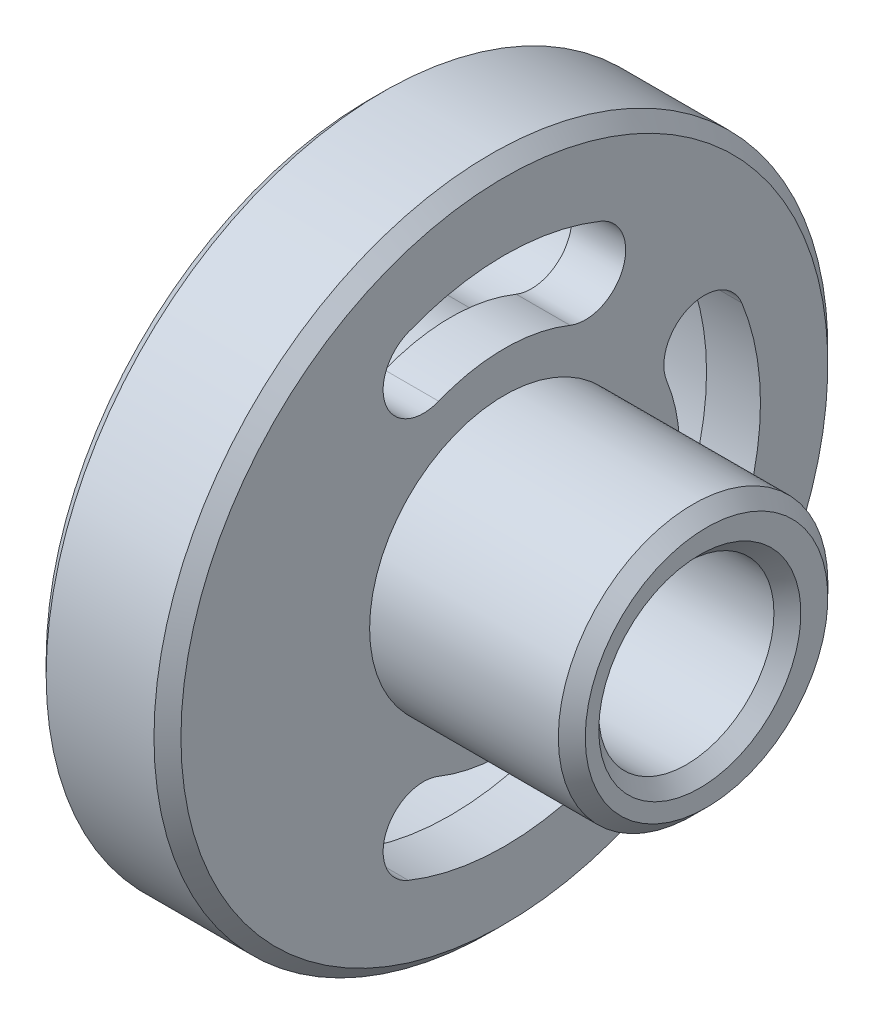
SolidWorks part; units mm, degrees
ref_plane "Спереди" through (0, 0, 0) normal (0, 0, 1) x (1, 0, 0)
ref_plane "Сверху" through (0, 0, 0) normal (0, 1, 0) x (1, 0, 0)
ref_plane "Справа" through (0, 0, 0) normal (1, 0, 0) x (0, 0, -1)
other "Configuration Table"
sketch "Эскиз1" plane through (0, 0, 0) normal (0, 0, 1) x (1, 0, 0)
  line L6 (0, 0) -> (24.4592, 0) construction
  line L7 (0, 0) -> (0, 24)
  line L8 (1, 25) -> (9, 25)
  line L9 (10, 24) -> (10, 10)
  line L10 (10, 10) -> (24, 10)
  line L11 (25, 9) -> (25, 0)
  line L12 (25, 0) -> (0, 0)
  line L13 (0, 24) -> (1, 25)
  line L14 (9, 25) -> (10, 24)
  line L15 (24, 10) -> (25, 9)
  point P4 (0, 25)
  point P5 (10, 25)
  point P7 (25, 10)
  dimension "D1" = 20
  dimension "D2" = 50
  dimension "D3" = 10
  dimension "D4" = 25
revolve "Повернуть1" add sketch "Эскиз1" angle 360 about L6
sketch "Эскиз3" plane through (25, 0, 0) normal (1, 0, 0) x (0, 0, -1)
  line L0 (0, 0) -> (8.7913, 0) construction
  circle A0 centre (-0.5, 0) radius 6.5
  dimension "D1" = 13
  dimension "D2" = 0.5
sketch "Эскиз4" plane through (0, 0, 0) normal (-1, 0, 0) x (0, 0, 1)
  line L0 (-8.7913, 0) -> (27.3062, 0) construction
  line L1 (0, 0) -> (0, 21.7955) construction
  line L2 (0, 0) -> (4.125, 10.1973) construction
  arc A0 (6, 14.8324) -> (-6, 14.8324) centre (0, 0) ccw construction
  arc A5 (7.875, 19.4675) -> (-7.875, 19.4675) centre (0, 0) ccw
  arc A6 (4.125, 10.1973) -> (-4.125, 10.1973) centre (0, 0) ccw
  arc A7 (4.125, 10.1973) -> (7.875, 19.4675) centre (6, 14.8324) ccw
  arc A8 (-7.875, 19.4675) -> (-4.125, 10.1973) centre (-6, 14.8324) ccw
  arc A9 (-10.1973, 4.125) -> (-10.1973, -4.125) centre (0, 0) ccw
  arc A10 (-10.1973, 4.125) -> (-19.4675, 7.875) centre (-14.8324, 6) ccw
  arc A11 (-19.4675, -7.875) -> (-10.1973, -4.125) centre (-14.8324, -6) ccw
  arc A12 (-19.4675, 7.875) -> (-19.4675, -7.875) centre (0, 0) ccw
  arc A13 (-14.8324, 6) -> (-14.8324, -6) centre (0, 0) ccw construction
  arc A14 (-4.125, -10.1973) -> (4.125, -10.1973) centre (0, 0) ccw
  arc A15 (-4.125, -10.1973) -> (-7.875, -19.4675) centre (-6, -14.8324) ccw
  arc A16 (7.875, -19.4675) -> (4.125, -10.1973) centre (6, -14.8324) ccw
  arc A17 (-7.875, -19.4675) -> (7.875, -19.4675) centre (0, 0) ccw
  arc A18 (-6, -14.8324) -> (6, -14.8324) centre (0, 0) ccw construction
  point P4 (0, 16)
  point P20 (-16, 0)
  point P27 (0, -16)
  dimension "D1" = 5
  dimension "D4" = 6
  dimension "D3" = 6
  dimension "D5" = 90
  dimension "D7" = 11
  dimension "D6" = 3
extrude "Вырез-Вытянуть2" cut sketch "Эскиз4" against normal blind 6
sketch "Эскиз5" plane through (0, 0, 0) normal (-1, 0, 0) x (0, 0, 1)
  line L0 (0, 0) -> (0, 21.7955) construction
  line L1 (0, 0) -> (4.875, 12.0513) construction
  arc A0 (6, 14.8324) -> (-6, 14.8324) centre (0, 0) ccw construction
  arc A1 (6, 14.8324) -> (-6, 14.8324) centre (0, 0) ccw construction
  arc A2 (7.125, 17.6135) -> (-7.125, 17.6135) centre (0, 0) ccw
  arc A3 (4.875, 12.0513) -> (-4.875, 12.0513) centre (0, 0) ccw
  arc A4 (4.875, 12.0513) -> (7.125, 17.6135) centre (6, 14.8324) ccw
  arc A5 (-7.125, 17.6135) -> (-4.875, 12.0513) centre (-6, 14.8324) ccw
  arc A6 (-12.0513, 4.875) -> (-12.0513, -4.875) centre (0, 0) ccw
  arc A7 (-12.0513, 4.875) -> (-17.6135, 7.125) centre (-14.8324, 6) ccw
  arc A8 (-17.6135, -7.125) -> (-12.0513, -4.875) centre (-14.8324, -6) ccw
  arc A9 (-17.6135, 7.125) -> (-17.6135, -7.125) centre (0, 0) ccw
  arc A10 (-14.8324, 6) -> (-14.8324, -6) centre (0, 0) ccw construction
  arc A11 (-4.875, -12.0513) -> (4.875, -12.0513) centre (0, 0) ccw
  arc A12 (-4.875, -12.0513) -> (-7.125, -17.6135) centre (-6, -14.8324) ccw
  arc A13 (7.125, -17.6135) -> (4.875, -12.0513) centre (6, -14.8324) ccw
  arc A14 (-7.125, -17.6135) -> (7.125, -17.6135) centre (0, 0) ccw
  arc A15 (-6, -14.8324) -> (6, -14.8324) centre (0, 0) ccw construction
  point P8 (0, 16)
  point P19 (-16, 0)
  point P26 (0, -16)
  dimension "D1" = 3
  dimension "D2" = 6
  dimension "D3" = 3
extrude "Вырез-Вытянуть3" cut sketch "Эскиз5" against normal through all
extrude "Вырез-Вытянуть4" cut sketch "Эскиз3" against normal blind 15 contours A0
chamfer "Фаска1" distance 1 angle 45 1 edges at (25, 0, -6)
